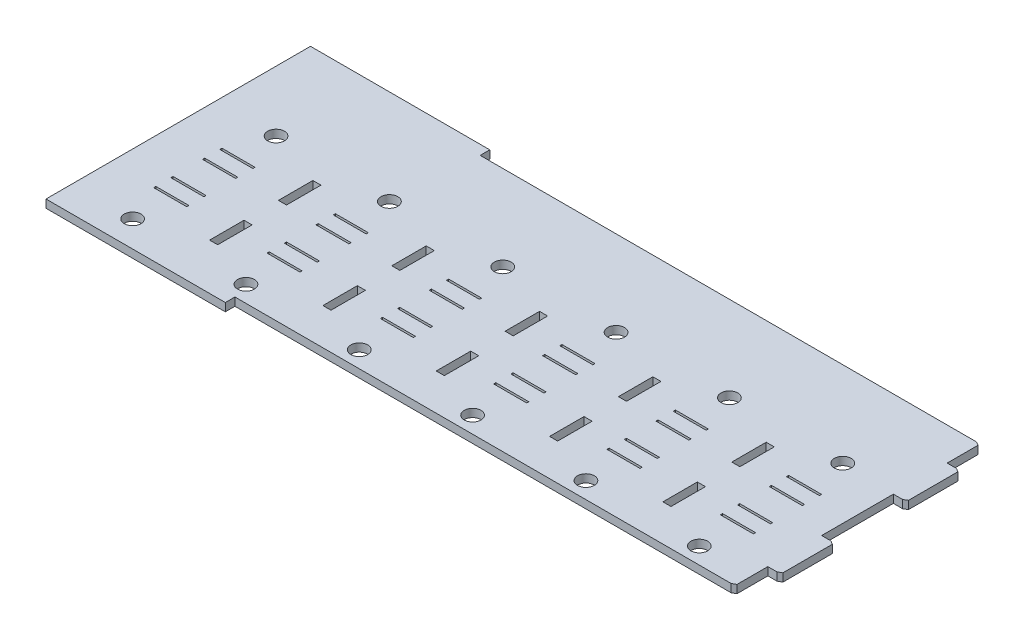
SolidWorks part; units mm, degrees
ref_plane "Front Plane" through (0, 0, 0) normal (0, 0, 1) x (1, 0, 0)
ref_plane "Top Plane" through (0, 0, 0) normal (0, 1, 0) x (1, 0, 0)
ref_plane "Right Plane" through (0, 0, 0) normal (1, 0, 0) x (0, 0, -1)
sketch "Sketch1" plane through (0, 0, 0) normal (0, 1, 0) x (1, 0, 0)
  line L1 (-122.555, 46.8266) -> (122.555, 46.8266)
  line L2 (-122.555, 46.8266) -> (-122.555, -46.8266)
  line L3 (-122.555, -46.8266) -> (122.555, -46.8266)
  line L4 (122.555, 46.8266) -> (122.555, -46.8266)
  line L5 (-122.555, 46.8266) -> (122.555, -46.8266) construction
  line L6 (-122.555, -46.8266) -> (122.555, 46.8266) construction
  point P0 (0, 0)
  dimension "D1" = 245.11
  dimension "D2" = 93.6531
extrude "Boss-Extrude1" add sketch "Sketch1" along normal blind 2.8575
sketch "Sketch2" plane through (0, 2.8575, 0) normal (0, 1, 0) x (1, 0, 0)
  line L0 (122.555, -46.8266) -> (122.555, 46.8266) construction
  line L1 (122.555, 46.8266) -> (-59.055, 46.8266) construction
  line L2 (122.555, 46.8266) -> (122.555, 43.4268) construction
  line L3 (122.555, 43.4268) -> (-59.055, 43.4268) construction
  line L4 (-59.055, 46.8266) -> (-59.055, 43.4268) construction
  line L5 (0, 0) -> (122.555, 0) construction
  line L6 (122.555, -43.4268) -> (-59.055, -43.4268) construction
  line L7 (122.555, -43.4268) -> (122.555, -46.8266) construction
  line L8 (122.555, -46.8266) -> (-59.055, -46.8266) construction
  line L9 (-59.055, -43.4268) -> (-59.055, -46.8266) construction
  line L11 (-122.555, 46.8266) -> (-122.555, -46.8266) construction
  line L12 (122.555, 46.8266) -> (-122.555, 46.8266) construction
  line L13 (122.555, 46.8266) -> (-59.055, 46.8266)
  line L14 (122.555, 46.8266) -> (122.555, 43.4268)
  line L15 (122.555, 43.4268) -> (-59.055, 43.4268)
  line L16 (-59.055, 46.8266) -> (-59.055, 43.4268)
  line L17 (122.555, -43.4268) -> (-59.055, -43.4268)
  line L18 (122.555, -43.4268) -> (122.555, -46.8266)
  line L19 (122.555, -46.8266) -> (-59.055, -46.8266)
  line L20 (-59.055, -43.4268) -> (-59.055, -46.8266)
  dimension "D1" = 86.8536
  dimension "D3" = 63.5
extrude "Cut-Extrude1" cut sketch "Sketch2" against normal up to next
sketch "Sketch4" plane through (0, 2.8575, 0) normal (0, 1, 0) x (1, 0, 0)
  line L0 (122.555, -43.4268) -> (122.555, 43.4268) construction
  line L1 (122.555, 43.4268) -> (117.983, 43.4268)
  line L2 (122.555, 43.4268) -> (122.555, 31.75)
  line L3 (122.555, 31.75) -> (117.983, 31.75)
  line L4 (117.983, 43.4268) -> (117.983, 31.75)
  line L5 (122.555, -43.4268) -> (117.983, -43.4268)
  line L6 (122.555, -43.4268) -> (122.555, -31.75)
  line L7 (122.555, -31.75) -> (117.983, -31.75)
  line L8 (117.983, -43.4268) -> (117.983, -31.75)
  line L9 (122.555, 12.7) -> (117.983, 12.7)
  line L10 (122.555, 12.7) -> (122.555, -12.7)
  line L11 (122.555, -12.7) -> (117.983, -12.7)
  line L12 (117.983, 12.7) -> (117.983, -12.7)
  line L13 (120.269, 12.7) -> (120.269, 31.75) construction
  line L14 (120.269, 22.225) -> (122.555, 22.225) construction
  line L15 (120.269, -12.7) -> (120.269, -31.75) construction
  line L16 (120.269, -22.225) -> (122.555, -22.225) construction
  dimension "D1" = 4.572
  dimension "D2" = 44.45
  dimension "D3" = 19.05
extrude "Cut-Extrude3" cut sketch "Sketch4" against normal up to next
sketch "Sketch5" plane through (0, 2.8575, 0) normal (0, 1, 0) x (1, 0, 0)
  line L0 (109.093, 34.5368) -> (109.093, 43.4268) construction
  line L1 (20.193, 34.5368) -> (109.093, 34.5368)
  line L2 (20.193, 34.5368) -> (20.193, -34.5368)
  line L3 (20.193, -34.5368) -> (109.093, -34.5368)
  line L4 (109.093, 34.5368) -> (109.093, -34.5368)
  line L5 (-59.055, 43.4268) -> (117.983, 43.4268) construction
  line L6 (109.093, -34.5368) -> (109.093, -43.4268) construction
  line L7 (117.983, -43.4268) -> (-59.055, -43.4268) construction
  line L8 (109.093, 0) -> (117.983, 0) construction
  line L10 (117.983, 31.75) -> (117.983, -31.75) construction
  dimension "D1" = 8.89
  dimension "D2" = 88.9
chamfer "Chamfer1" [suppressed] distance 3.175 angle 45
chamfer "Chamfer2" distance 0.762 angle 60 3 edges at (117.983, 1.4287, 43.4268) (122.555, 1.4287, 31.75) (122.555, 1.4287, -12.7)
chamfer "Chamfer3" distance 0.762 angle 60 3 edges at (122.555, 1.4287, -31.75) (117.983, 1.4287, -43.4268) (122.555, 1.4287, 12.7)
fillet "Fillet2" [suppressed] radius 0.762
sketch "Sketch6" plane through (0, 2.8575, 0) normal (0, 1, 0) x (1, 0, 0)
  line L0 (117.983, 42.6648) -> (116.6632, 43.4268) construction
  line L1 (42.2764, -42.6648) -> (42.2764, 18.2952)
  line L2 (116.6632, 43.4268) -> (116.6632, 42.6648) construction
  line L3 (116.6632, 42.6648) -> (117.983, 42.6648) construction
  line L4 (116.6632, 43.4268) -> (-122.555, 43.4268) construction
  line L5 (-122.555, 46.8266) -> (-122.555, -46.8266) construction
  line L6 (116.6632, -43.4268) -> (117.983, -42.6648) construction
  line L7 (117.983, -42.6648) -> (116.6632, -42.6648) construction
  line L8 (116.6632, -42.6648) -> (116.6632, -43.4268) construction
  line L9 (116.6632, -43.4268) -> (117.983, -42.6648) construction
  line L10 (116.6632, 42.6648) -> (116.6632, -42.6648) construction
  line L11 (116.6632, -42.6648) -> (-122.555, -42.6648) construction
  line L12 (-122.555, -42.6648) -> (-122.555, 43.4268) construction
  line L13 (76.5363, 18.2952) -> (42.2764, 18.2952)
  line L14 (116.6632, -42.6648) -> (82.4033, -42.6648)
  line L15 (116.6632, -42.6648) -> (116.6632, 18.2952)
  line L16 (116.6632, 18.2952) -> (82.4033, 18.2952)
  line L17 (82.4033, -42.6648) -> (82.4033, 18.2952)
  line L18 (76.5363, -42.6648) -> (76.5363, 18.2952)
  line L19 (76.5363, -42.6648) -> (42.2764, -42.6648)
  line L20 (2.1495, -42.6648) -> (2.1495, 18.2952)
  line L21 (36.4094, 18.2952) -> (2.1495, 18.2952)
  line L22 (36.4094, -42.6648) -> (36.4094, 18.2952)
  line L23 (36.4094, -42.6648) -> (2.1495, -42.6648)
  line L24 (-37.9774, -42.6648) -> (-37.9774, 18.2952)
  line L25 (-3.7175, 18.2952) -> (-37.9774, 18.2952)
  line L26 (-3.7175, -42.6648) -> (-3.7175, 18.2952)
  line L27 (-3.7175, -42.6648) -> (-37.9774, -42.6648)
  line L28 (-78.1042, -42.6648) -> (-78.1042, 18.2952)
  line L29 (-43.8443, 18.2952) -> (-78.1042, 18.2952)
  line L30 (-43.8443, -42.6648) -> (-43.8443, 18.2952)
  line L31 (-43.8443, -42.6648) -> (-78.1042, -42.6648)
  line L32 (-118.2311, -42.6648) -> (-118.2311, 18.2952)
  line L33 (-83.9712, 18.2952) -> (-118.2311, 18.2952)
  line L34 (-83.9712, -42.6648) -> (-83.9712, 18.2952)
  line L35 (-83.9712, -42.6648) -> (-118.2311, -42.6648)
  line L36 (99.5332, 18.2952) -> (116.6632, 18.2952) construction
  line L37 (108.0982, 18.2952) -> (108.0982, 43.4268) construction
  line L38 (116.6632, -42.6648) -> (82.4033, 18.2952) construction
  line L39 (76.5363, 18.2952) -> (42.2764, -42.6648) construction
  line L40 (36.4094, -42.6648) -> (2.1495, 18.2952) construction
  line L41 (-3.7175, 18.2952) -> (-37.9774, -42.6648) construction
  line L42 (-43.8443, -42.6648) -> (-78.1042, 18.2952) construction
  line L43 (-83.9712, 18.2952) -> (-118.2311, -42.6648) construction
  line L44 (99.5332, -12.1848) -> (99.5332, -6.5714) construction
  line L45 (99.5332, -6.5714) -> (99.5332, -0.4754) construction
  line L46 (105.3752, -6.1904) -> (93.6912, -6.1904)
  line L47 (105.3752, -6.1904) -> (105.3752, -6.9524)
  line L48 (105.3752, -6.9524) -> (93.6912, -6.9524)
  line L49 (93.6912, -6.1904) -> (93.6912, -6.9524)
  line L50 (105.3752, -6.1904) -> (93.6912, -6.9524) construction
  line L51 (105.3752, -6.9524) -> (93.6912, -6.1904) construction
  line L52 (105.3752, -6.9524) -> (105.3752, -17.4213) construction
  line L53 (93.6912, -0.0944) -> (105.3752, -0.0944)
  line L54 (93.6912, -0.0944) -> (93.6912, -0.8564)
  line L55 (93.6912, -0.8564) -> (105.3752, -0.8564)
  line L56 (105.3752, -0.0944) -> (105.3752, -0.8564)
  line L57 (93.6912, -0.0944) -> (105.3752, -0.8564) construction
  line L58 (93.6912, -0.8564) -> (105.3752, -0.0944) construction
  line L59 (105.3752, -18.1833) -> (93.6912, -17.4213) construction
  line L60 (105.3752, -17.4213) -> (93.6912, -17.4213)
  line L61 (105.3752, -17.4213) -> (105.3752, -18.1833)
  line L62 (105.3752, -18.1833) -> (93.6912, -18.1833)
  line L63 (93.6912, -17.4213) -> (93.6912, -18.1833)
  line L64 (99.5332, -17.8023) -> (99.5332, -23.8983) construction
  line L65 (59.4064, -12.1848) -> (65.2484, -12.1848) construction
  line L66 (105.3752, -24.2793) -> (93.6912, -24.2793)
  line L67 (105.3752, -24.2793) -> (105.3752, -23.5173)
  line L68 (105.3752, -23.5173) -> (93.6912, -23.5173)
  line L69 (93.6912, -24.2793) -> (93.6912, -23.5173)
  line L70 (105.3752, -24.2793) -> (93.6912, -23.5173) construction
  line L71 (105.3752, -23.5173) -> (93.6912, -24.2793) construction
  line L72 (105.3752, -12.1869) -> (65.2484, -12.1848) construction
  line L73 (65.2432, -6.1904) -> (53.5592, -6.1904)
  line L74 (65.2432, -6.1904) -> (65.2432, -6.9524)
  line L75 (65.2432, -6.9524) -> (53.5592, -6.9524)
  line L76 (53.5592, -6.1904) -> (53.5592, -6.9524)
  line L77 (53.5592, -0.0944) -> (65.2432, -0.0944)
  line L78 (53.5592, -0.0944) -> (53.5592, -0.8564)
  line L79 (53.5592, -0.8564) -> (65.2432, -0.8564)
  line L80 (65.2432, -0.0944) -> (65.2432, -0.8564)
  line L81 (65.2432, -17.4213) -> (53.5592, -17.4213)
  line L82 (65.2432, -17.4213) -> (65.2432, -18.1833)
  line L83 (65.2432, -18.1833) -> (53.5592, -18.1833)
  line L84 (53.5592, -17.4213) -> (53.5592, -18.1833)
  line L85 (65.2432, -24.2793) -> (53.5592, -24.2793)
  line L86 (65.2432, -24.2793) -> (65.2432, -23.5173)
  line L87 (65.2432, -23.5173) -> (53.5592, -23.5173)
  line L88 (53.5592, -24.2793) -> (53.5592, -23.5173)
  line L89 (59.4012, -12.1848) -> (59.4012, -6.5714) construction
  line L90 (59.4012, -6.5714) -> (59.4012, -0.4754) construction
  line L91 (65.2432, -6.1904) -> (53.5592, -6.9524) construction
  line L92 (65.2432, -6.9524) -> (53.5592, -6.1904) construction
  line L93 (65.2432, -6.9524) -> (65.2432, -17.4213) construction
  line L94 (53.5592, -0.0944) -> (65.2432, -0.8564) construction
  line L95 (53.5592, -0.8564) -> (65.2432, -0.0944) construction
  line L96 (65.2432, -18.1833) -> (53.5592, -17.4213) construction
  line L97 (59.4012, -17.8023) -> (59.4012, -23.8983) construction
  line L98 (65.2432, -24.2793) -> (53.5592, -23.5173) construction
  line L99 (65.2432, -23.5173) -> (53.5592, -24.2793) construction
  line L100 (25.1112, -6.1904) -> (13.4272, -6.1904)
  line L101 (25.1112, -6.1904) -> (25.1112, -6.9524)
  line L102 (25.1112, -6.9524) -> (13.4272, -6.9524)
  line L103 (13.4272, -6.1904) -> (13.4272, -6.9524)
  line L104 (13.4272, -0.0944) -> (25.1112, -0.0944)
  line L105 (13.4272, -0.0944) -> (13.4272, -0.8564)
  line L106 (13.4272, -0.8564) -> (25.1112, -0.8564)
  line L107 (25.1112, -0.0944) -> (25.1112, -0.8564)
  line L108 (25.1112, -17.4213) -> (13.4272, -17.4213)
  line L109 (25.1112, -17.4213) -> (25.1112, -18.1833)
  line L110 (25.1112, -18.1833) -> (13.4272, -18.1833)
  line L111 (13.4272, -17.4213) -> (13.4272, -18.1833)
  line L112 (25.1112, -24.2793) -> (13.4272, -24.2793)
  line L113 (25.1112, -24.2793) -> (25.1112, -23.5173)
  line L114 (25.1112, -23.5173) -> (13.4272, -23.5173)
  line L115 (13.4272, -24.2793) -> (13.4272, -23.5173)
  line L116 (19.2692, -12.1848) -> (19.2692, -6.5714) construction
  line L117 (19.2692, -6.5714) -> (19.2692, -0.4754) construction
  line L118 (25.1112, -6.1904) -> (13.4272, -6.9524) construction
  line L119 (25.1112, -6.9524) -> (13.4272, -6.1904) construction
  line L120 (25.1112, -6.9524) -> (25.1112, -17.4213) construction
  line L121 (13.4272, -0.0944) -> (25.1112, -0.8564) construction
  line L122 (13.4272, -0.8564) -> (25.1112, -0.0944) construction
  line L123 (25.1112, -18.1833) -> (13.4272, -17.4213) construction
  line L124 (19.2692, -17.8023) -> (19.2692, -23.8983) construction
  line L125 (25.1112, -24.2793) -> (13.4272, -23.5173) construction
  line L126 (25.1112, -23.5173) -> (13.4272, -24.2793) construction
  line L127 (-15.0208, -6.1904) -> (-26.7048, -6.1904)
  line L128 (-15.0208, -6.1904) -> (-15.0208, -6.9524)
  line L129 (-15.0208, -6.9524) -> (-26.7048, -6.9524)
  line L130 (-26.7048, -6.1904) -> (-26.7048, -6.9524)
  line L131 (-26.7048, -0.0944) -> (-15.0208, -0.0944)
  line L132 (-26.7048, -0.0944) -> (-26.7048, -0.8564)
  line L133 (-26.7048, -0.8564) -> (-15.0208, -0.8564)
  line L134 (-15.0208, -0.0944) -> (-15.0208, -0.8564)
  line L135 (-15.0208, -17.4213) -> (-26.7048, -17.4213)
  line L136 (-15.0208, -17.4213) -> (-15.0208, -18.1833)
  line L137 (-15.0208, -18.1833) -> (-26.7048, -18.1833)
  line L138 (-26.7048, -17.4213) -> (-26.7048, -18.1833)
  line L139 (-15.0208, -24.2793) -> (-26.7048, -24.2793)
  line L140 (-15.0208, -24.2793) -> (-15.0208, -23.5173)
  line L141 (-15.0208, -23.5173) -> (-26.7048, -23.5173)
  line L142 (-26.7048, -24.2793) -> (-26.7048, -23.5173)
  line L143 (-20.8628, -12.1848) -> (-20.8628, -6.5714) construction
  line L144 (-20.8628, -6.5714) -> (-20.8628, -0.4754) construction
  line L145 (-15.0208, -6.1904) -> (-26.7048, -6.9524) construction
  line L146 (-15.0208, -6.9524) -> (-26.7048, -6.1904) construction
  line L147 (-15.0208, -6.9524) -> (-15.0208, -17.4213) construction
  line L148 (-26.7048, -0.0944) -> (-15.0208, -0.8564) construction
  line L149 (-26.7048, -0.8564) -> (-15.0208, -0.0944) construction
  line L150 (-15.0208, -18.1833) -> (-26.7048, -17.4213) construction
  line L151 (-20.8628, -17.8023) -> (-20.8628, -23.8983) construction
  line L152 (-15.0208, -24.2793) -> (-26.7048, -23.5173) construction
  line L153 (-15.0208, -23.5173) -> (-26.7048, -24.2793) construction
  line L154 (-55.1528, -6.1904) -> (-66.8368, -6.1904)
  line L155 (-55.1528, -6.1904) -> (-55.1528, -6.9524)
  line L156 (-55.1528, -6.9524) -> (-66.8368, -6.9524)
  line L157 (-66.8368, -6.1904) -> (-66.8368, -6.9524)
  line L158 (-66.8368, -0.0944) -> (-55.1528, -0.0944)
  line L159 (-66.8368, -0.0944) -> (-66.8368, -0.8564)
  line L160 (-66.8368, -0.8564) -> (-55.1528, -0.8564)
  line L161 (-55.1528, -0.0944) -> (-55.1528, -0.8564)
  line L162 (-55.1528, -17.4213) -> (-66.8368, -17.4213)
  line L163 (-55.1528, -17.4213) -> (-55.1528, -18.1833)
  line L164 (-55.1528, -18.1833) -> (-66.8368, -18.1833)
  line L165 (-66.8368, -17.4213) -> (-66.8368, -18.1833)
  line L166 (-55.1528, -24.2793) -> (-66.8368, -24.2793)
  line L167 (-55.1528, -24.2793) -> (-55.1528, -23.5173)
  line L168 (-55.1528, -23.5173) -> (-66.8368, -23.5173)
  line L169 (-66.8368, -24.2793) -> (-66.8368, -23.5173)
  line L170 (-60.9948, -12.1848) -> (-60.9948, -6.5714) construction
  line L171 (-60.9948, -6.5714) -> (-60.9948, -0.4754) construction
  line L172 (-55.1528, -6.1904) -> (-66.8368, -6.9524) construction
  line L173 (-55.1528, -6.9524) -> (-66.8368, -6.1904) construction
  line L174 (-55.1528, -6.9524) -> (-55.1528, -17.4213) construction
  line L175 (-66.8368, -0.0944) -> (-55.1528, -0.8564) construction
  line L176 (-66.8368, -0.8564) -> (-55.1528, -0.0944) construction
  line L177 (-55.1528, -18.1833) -> (-66.8368, -17.4213) construction
  line L178 (-60.9948, -17.8023) -> (-60.9948, -23.8983) construction
  line L179 (-55.1528, -24.2793) -> (-66.8368, -23.5173) construction
  line L180 (-55.1528, -23.5173) -> (-66.8368, -24.2793) construction
  line L181 (-95.2848, -6.1904) -> (-106.9688, -6.1904)
  line L182 (-95.2848, -6.1904) -> (-95.2848, -6.9524)
  line L183 (-95.2848, -6.9524) -> (-106.9688, -6.9524)
  line L184 (-106.9688, -6.1904) -> (-106.9688, -6.9524)
  line L185 (-106.9688, -0.0944) -> (-95.2848, -0.0944)
  line L186 (-106.9688, -0.0944) -> (-106.9688, -0.8564)
  line L187 (-106.9688, -0.8564) -> (-95.2848, -0.8564)
  line L188 (-95.2848, -0.0944) -> (-95.2848, -0.8564)
  line L189 (-95.2848, -17.4213) -> (-106.9688, -17.4213)
  line L190 (-95.2848, -17.4213) -> (-95.2848, -18.1833)
  line L191 (-95.2848, -18.1833) -> (-106.9688, -18.1833)
  line L192 (-106.9688, -17.4213) -> (-106.9688, -18.1833)
  line L193 (-95.2848, -24.2793) -> (-106.9688, -24.2793)
  line L194 (-95.2848, -24.2793) -> (-95.2848, -23.5173)
  line L195 (-95.2848, -23.5173) -> (-106.9688, -23.5173)
  line L196 (-106.9688, -24.2793) -> (-106.9688, -23.5173)
  line L197 (-101.1268, -12.1848) -> (-101.1268, -6.5714) construction
  line L198 (-101.1268, -6.5714) -> (-101.1268, -0.4754) construction
  line L199 (-95.2848, -6.1904) -> (-106.9688, -6.9524) construction
  line L200 (-95.2848, -6.9524) -> (-106.9688, -6.1904) construction
  line L201 (-95.2848, -6.9524) -> (-95.2848, -17.4213) construction
  line L202 (-106.9688, -0.0944) -> (-95.2848, -0.8564) construction
  line L203 (-106.9688, -0.8564) -> (-95.2848, -0.0944) construction
  line L204 (-95.2848, -18.1833) -> (-106.9688, -17.4213) construction
  line L205 (-101.1268, -17.8023) -> (-101.1268, -23.8983) construction
  line L206 (-95.2848, -24.2793) -> (-106.9688, -23.5173) construction
  line L207 (-95.2848, -23.5173) -> (-106.9688, -24.2793) construction
  text T0 "Line"
  dimension "D1" = 60.96
  dimension "D2" = 6
  dimension "D3" = 5.6134
  dimension "D4" = 0.762
  dimension "D5" = 11.684
  dimension "D6" = 6.096
  dimension "D7" = 0.762
  dimension "D8" = 11.684
  dimension "D9" = 10.4689
  dimension "D10" = 0.762
  dimension "D11" = 6.096
  dimension "D12" = 0.762
  dimension "D13" = 5.842
  dimension "D14" = 6
extrude "Cut-Extrude4" cut sketch "Sketch6" against normal through all contours L56 L53 L54 L55 | L46 L49 L48 L47 | L60 L63 L62 L61 | L69 L66 L67 L68 | L80 L77 L78 L79 | L73 L76 L75 L74 | L81 L84 L83 L82 | L88 L85 L86 L87 | L107 L104 L105 L106 | L100 L103 L102 L101 | L108 L111 L110 L109 | L115 L112 L113 L114 | L134 L131 L132 L133 | L127 L130 L129 L128 | L135 L138 L137 L136 | L142 L139 L140 L141 | L161 L158 L159 L160 | L154 L157 L156 L155 | L162 L165 L164 L163 | L169 L166 L167 L168 | L188 L185 L186 L187 | L181 L184 L183 L182 | L189 L192 L191 L190 | L196 L193 L194 L195
sketch "Sketch9" plane through (0, 2.8575, 0) normal (0, 1, 0) x (1, 0, 0)
  line L0 (82.4033, 18.2952) -> (76.5363, 18.2952) construction
  line L1 (76.5363, -42.6648) -> (82.4033, 18.2952) construction
  line L2 (76.5363, -42.6648) -> (82.4033, -42.6648) construction
  line L3 (82.4033, -42.6648) -> (82.4033, 18.2952) construction
  line L5 (79.4698, -12.1848) -> (80.9771, -12.1848) construction
  line L6 (80.9771, -12.1848) -> (80.9771, 0.0072) construction
  line L7 (42.2764, 18.2952) -> (36.4094, 18.2952) construction
  line L12 (80.9771, -12.1848) -> (80.9771, -24.3768) construction
  line L13 (82.4084, 6.1032) -> (79.5458, 6.1032)
  line L18 (82.4084, 6.1032) -> (82.4084, -6.0888)
  line L19 (82.4084, -6.0888) -> (79.5458, -6.0888)
  line L20 (36.4094, 18.2952) -> (36.4094, -42.6648) construction
  line L21 (36.4094, -42.6648) -> (42.2764, -42.6648) construction
  line L22 (42.2764, -42.6648) -> (42.2764, 18.2952) construction
  line L23 (42.2764, 18.2952) -> (36.4094, -42.6648) construction
  line L24 (42.2764, 6.1032) -> (39.4138, 6.1032)
  line L33 (42.2764, 6.1032) -> (42.2764, -6.0888)
  line L34 (42.2764, -6.0888) -> (39.4138, -6.0888)
  line L35 (39.4138, 6.1032) -> (39.4138, -6.0888)
  line L36 (42.2764, -30.4728) -> (39.4138, -30.4728)
  line L37 (42.2764, -30.4728) -> (42.2764, -18.2808)
  line L38 (42.2764, -18.2808) -> (39.4138, -18.2808)
  line L47 (39.4138, -30.4728) -> (39.4138, -18.2808)
  line L48 (39.3378, -12.1848) -> (40.8451, -12.1848) construction
  line L49 (40.8451, -12.1848) -> (40.8451, 0.0072) construction
  line L50 (40.8451, -12.1848) -> (40.8451, -24.3768) construction
  line L51 (42.2764, 6.1032) -> (39.4138, -6.0888) construction
  line L52 (42.2764, -6.0888) -> (39.4138, 6.1032) construction
  line L61 (42.2764, -30.4728) -> (39.4138, -18.2808) construction
  line L62 (42.2764, -18.2808) -> (39.4138, -30.4728) construction
  line L63 (2.1444, 6.1032) -> (-0.7182, 6.1032)
  line L64 (2.1444, 6.1032) -> (2.1444, -6.0888)
  line L65 (2.1444, -6.0888) -> (-0.7182, -6.0888)
  line L66 (-0.7182, 6.1032) -> (-0.7182, -6.0888)
  line L75 (2.1444, -30.4728) -> (-0.7182, -30.4728)
  line L76 (2.1444, -30.4728) -> (2.1444, -18.2808)
  line L77 (2.1444, -18.2808) -> (-0.7182, -18.2808)
  line L78 (-0.7182, -30.4728) -> (-0.7182, -18.2808)
  line L79 (-0.7942, -12.1848) -> (0.7131, -12.1848) construction
  line L80 (0.7131, -12.1848) -> (0.7131, 0.0072) construction
  line L81 (79.5458, 6.1032) -> (79.5458, -6.0888)
  line L82 (82.4084, 6.1032) -> (79.5458, -6.0888) construction
  line L83 (82.4084, -6.0888) -> (79.5458, 6.1032) construction
  line L84 (0.7131, -12.1848) -> (0.7131, -24.3768) construction
  line L85 (82.4084, -30.4728) -> (79.5458, -30.4728)
  line L86 (82.4084, -30.4728) -> (82.4084, -18.2808)
  line L87 (82.4084, -18.2808) -> (79.5458, -18.2808)
  line L88 (79.5458, -30.4728) -> (79.5458, -18.2808)
  line L89 (82.4084, -30.4728) -> (79.5458, -18.2808) construction
  line L90 (82.4084, -18.2808) -> (79.5458, -30.4728) construction
  line L91 (2.1444, 6.1032) -> (-0.7182, -6.0888) construction
  line L92 (2.1444, -6.0888) -> (-0.7182, 6.1032) construction
  line L93 (2.1444, -30.4728) -> (-0.7182, -18.2808) construction
  line L94 (2.1444, -18.2808) -> (-0.7182, -30.4728) construction
  line L95 (-37.9876, 6.1032) -> (-40.8502, 6.1032)
  line L96 (-37.9876, 6.1032) -> (-37.9876, -6.0888)
  line L97 (-37.9876, -6.0888) -> (-40.8502, -6.0888)
  line L98 (-40.8502, 6.1032) -> (-40.8502, -6.0888)
  line L99 (-37.9876, -30.4728) -> (-40.8502, -30.4728)
  line L100 (-37.9876, -30.4728) -> (-37.9876, -18.2808)
  line L101 (-37.9876, -18.2808) -> (-40.8502, -18.2808)
  line L102 (-40.8502, -30.4728) -> (-40.8502, -18.2808)
  line L103 (-40.9262, -12.1848) -> (-39.4189, -12.1848) construction
  line L104 (-39.4189, -12.1848) -> (-39.4189, 0.0072) construction
  line L105 (-39.4189, -12.1848) -> (-39.4189, -24.3768) construction
  line L106 (-37.9876, 6.1032) -> (-40.8502, -6.0888) construction
  line L107 (-37.9876, -6.0888) -> (-40.8502, 6.1032) construction
  line L108 (-37.9876, -30.4728) -> (-40.8502, -18.2808) construction
  line L109 (-37.9876, -18.2808) -> (-40.8502, -30.4728) construction
  line L110 (-78.1196, 6.1032) -> (-80.9822, 6.1032)
  line L111 (-78.1196, 6.1032) -> (-78.1196, -6.0888)
  line L112 (-78.1196, -6.0888) -> (-80.9822, -6.0888)
  line L113 (-80.9822, 6.1032) -> (-80.9822, -6.0888)
  line L114 (-78.1196, -30.4728) -> (-80.9822, -30.4728)
  line L115 (-78.1196, -30.4728) -> (-78.1196, -18.2808)
  line L116 (-78.1196, -18.2808) -> (-80.9822, -18.2808)
  line L117 (-80.9822, -30.4728) -> (-80.9822, -18.2808)
  line L118 (-81.0582, -12.1848) -> (-79.5509, -12.1848) construction
  line L119 (-79.5509, -12.1848) -> (-79.5509, 0.0072) construction
  line L120 (-79.5509, -12.1848) -> (-79.5509, -24.3768) construction
  line L121 (-78.1196, 6.1032) -> (-80.9822, -6.0888) construction
  line L122 (-78.1196, -6.0888) -> (-80.9822, 6.1032) construction
  line L123 (-78.1196, -30.4728) -> (-80.9822, -18.2808) construction
  line L124 (-78.1196, -18.2808) -> (-80.9822, -30.4728) construction
  line L125 (76.5363, 6.1032) -> (76.5363, -30.4728) construction
  dimension "D1" = 1.5073
  dimension "D2" = 12.192
  dimension "D3" = 12.192
  dimension "D4" = 2.8626
  dimension "D5" = 12.192
  dimension "D6" = 12.192
  dimension "D7" = 5
  dimension "D8" = 2.8626
extrude "Cut-Extrude5" cut sketch "Sketch9" against normal through all
sketch "Sketch11" plane through (0, 2.8575, 0) normal (0, 1, 0) x (1, 0, 0)
  line L0 (99.5332, -12.1848) -> (99.5332, -37.5848) construction
  line L1 (99.5332, -12.1848) -> (99.5332, 13.2152) construction
  circle A0 centre (99.5332, 13.2152) radius 2.975
  circle A1 centre (99.5332, -37.5848) radius 2.975
  circle A2 centre (59.4012, -37.5848) radius 2.975
  circle A3 centre (59.4012, 13.2152) radius 2.975
  circle A4 centre (19.2692, -37.5848) radius 2.975
  circle A5 centre (19.2692, 13.2152) radius 2.975
  circle A6 centre (-20.8628, -37.5848) radius 2.975
  circle A7 centre (-20.8628, 13.2152) radius 2.975
  circle A8 centre (-60.9948, -37.5848) radius 2.975
  circle A9 centre (-60.9948, 13.2152) radius 2.975
  circle A10 centre (-101.1268, -37.5848) radius 2.975
  circle A11 centre (-101.1268, 13.2152) radius 2.975
  dimension "D3" = 6
  dimension "D1" = 25.4
  dimension "D2" = 25.4
extrude "Cut-Extrude6" cut sketch "Sketch11" against normal through all
